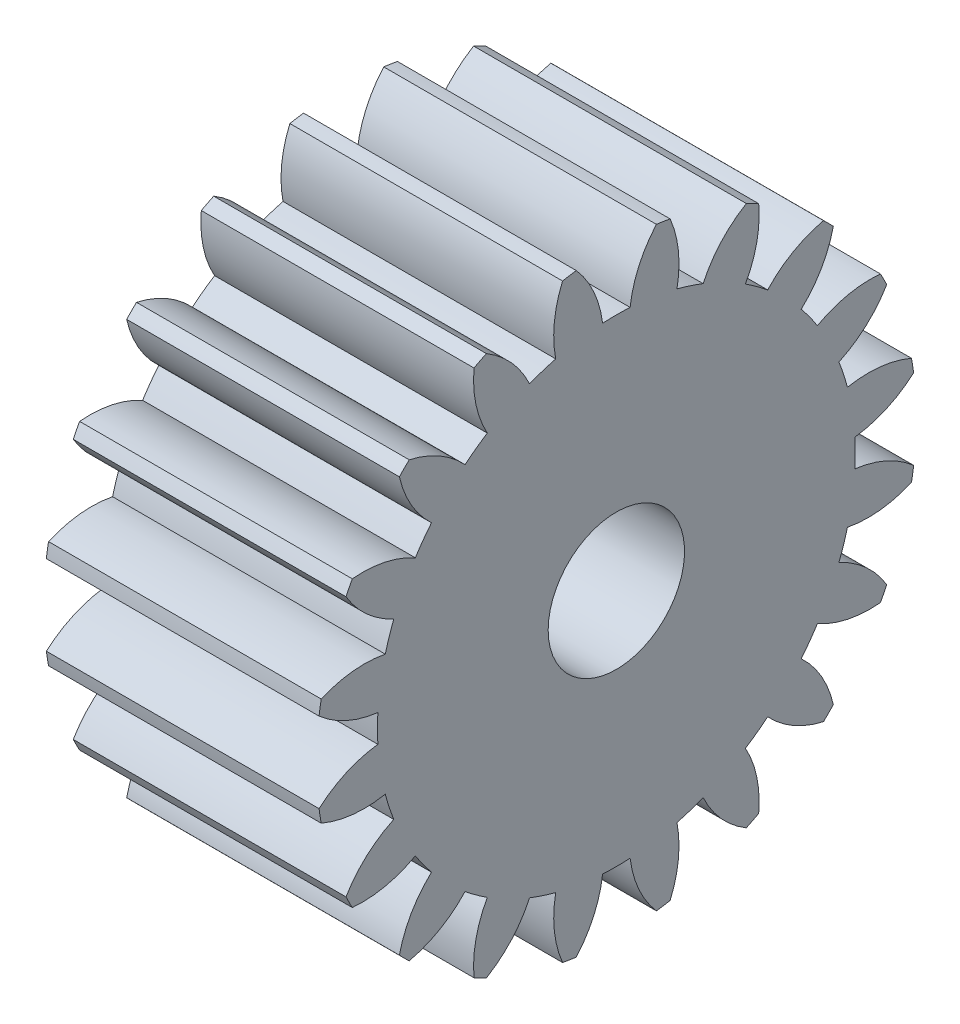
SolidWorks part; units mm, degrees
ref_plane "Plane1" through (0, 0, 0) normal (0, 0, 1) x (1, 0, 0)
ref_plane "Plane2" through (0, 0, 0) normal (0, 1, 0) x (1, 0, 0)
ref_plane "Plane3" through (0, 0, 0) normal (1, 0, 0) x (0, 0, -1)
sketch "HoldingSke" plane through (0, 0, 0) normal (0, 1, 0) x (1, 0, 0)
  line L0 (0, 0) -> (477.3639, -173.7462)
  line L1 (-15, 0) -> (100, 0) construction
  line L2 (0, 0) -> (-2.1039, 2.3779)
  line L3 (0, 0) -> (-11.863, 4.5341)
  line L4 (0, 0) -> (8.1152, 2.9537)
  line L5 (0, 0) -> (-47.5972, -17.7524)
  line L6 (0, 0) -> (-10.5278, -7.1032)
  line L7 (-2.1039, 2.3779) -> (8.8308, 51.9871)
  line L8 (-76.2, 54.61) -> (-69.596, 54.61)
  line L9 (-71.009, 38.7566) -> (-53.1078, 45.2721)
  line L10 (-76.2, 71.12) -> (104.1128, 71.12)
  line L11 (0, 0) -> (-12.7, 0)
  line L12 (-76.2, 101.6) -> (-76.1492, 101.6)
  line L13 (24.9733, 27.94) -> (52.9518, 28.4284)
  line L14 (24.9733, 27.94) -> (25.0241, 27.9398)
  line L15 (24.9733, 27.94) -> (100.4021, 29.52)
  circle A0 centre (0, 0) radius 3.175
  circle A1 centre (0, 0) radius 11.1252
  circle A2 centre (0, 0) radius 38.1
  circle A3 centre (0, 0) radius 3.175
  dimension "Hub_dia" = 76.2
  dimension "Pitch" = 508
  dimension "Overall_len" = 50.8
  dimension "OAL" = 50.8001
  dimension "Ap" = 20
  dimension "H" = 19.05
  dimension "Pitch_radius" = 180.3128
  dimension "Backlash" = 0.0508
  dimension "Addendum_fac" = 1
  dimension "Dedendum_fac" = 1.2
  dimension "Clearance_fac" = 0.2
  dimension "Dedendum_add" = 0.0508
sketch "BasProSke" plane through (0, 0, 0) normal (0, 1, 0) x (1, 0, 0)
  line L0 (-10, 0) -> (60, 0) construction
  line L1 (0, 0) -> (0, 13.97)
  line L2 (0, 0) -> (12.7, 0)
  line L3 (12.7, 0) -> (12.7, 13.97)
  line L4 (12.7, 13.97) -> (0, 13.97)
revolve "Base-Revolve" add sketch "BasProSke" angle 360 about L0
sketch "TooCutSke" plane through (0, 0, 0) normal (1, 0, 0) x (0, 0, -1)
  line L1 (0, 0) -> (0, 107) construction
  line L2 (0, 0) -> (-1.0853, 12.6535) construction
  line L3 (0, 0) -> (-3.9633, 25.0231) construction
  line L4 (-1.0853, 12.6535) -> (-1.9816, 12.5116) construction
  arc A0 (0.6405, 11.1067) -> (-0.6405, 11.1067) centre (0, 0) ccw
  arc A1 (1.8856, 13.8678) -> (-1.8856, 13.8678) centre (0, 0) ccw
  circle A2 centre (0, 0) radius 12.7 construction
  circle A3 centre (0, 0) radius 11.9341 construction
  arc A4 (-0.6405, 11.1067) -> (-1.8856, 13.8678) centre (-5.6834, 10.4939) ccw
  arc A5 (1.8856, 13.8678) -> (0.6405, 11.1067) centre (5.6834, 10.4939) ccw
extrude "ToothCut" cut sketch "TooCutSke" along normal through all
fillet "Breaks" [suppressed] radius 0.0254
fillet "RootFillets" [suppressed] radius 0.3048
pattern_circular "TeethCuts" count 20 every 18 about axis through (-10, 0, 0) along (1, 0, 0) of "ToothCut", "RootFillets", "Breaks"
sketch "HubNeaOneSke" plane through (0, 0, 0) normal (-1, 0, 0) x (0, 0, 1)
  circle A0 centre (0, 0) radius 11.1252
extrude "HubNearOne" [suppressed] add sketch "HubNeaOneSke" along normal blind 38.1001
sketch "HubNeaBotSke" plane through (0, 0, 0) normal (-1, 0, 0) x (0, 0, 1)
  circle A0 centre (0, 0) radius 11.1252
extrude "HubNearBoth" [suppressed] add sketch "HubNeaBotSke" along normal blind 19.05
ref_plane "FarPln" through (12.7, 0, 0) normal (1, 0, 0) x (0, 0, -1)
sketch "HubFarSke" plane through (12.7, 0, 0) normal (1, 0, 0) x (0, 0, -1)
  circle A0 centre (0, 0) radius 11.1252
extrude "HubFar" [suppressed] add sketch "HubFarSke" along normal blind 19.05
sketch "BorSke" plane through (0, 0, 0) normal (1, 0, 0) x (0, 0, -1)
  circle A0 centre (0, 0) radius 3.175
extrude "Bore" cut sketch "BorSke" along normal mid plane 101.6001
sketch "KeySke" plane through (0, 0, 0) normal (1, 0, 0) x (0, 0, -1)
  line L0 (-0.127, 0) -> (-0.127, 3.429)
  line L1 (-0.127, 3.429) -> (0.127, 3.429)
  line L2 (0.127, 3.429) -> (0.127, 0)
  line L3 (0, 0) -> (0, 34) construction
  line L4 (-0.127, 0) -> (0.127, 0)
  dimension "Width" = 0.254
extrude "Keyway" [suppressed] cut sketch "KeySke" along normal mid plane 101.6001
pattern_circular "Keyway2" [suppressed] count 2 every 90 about axis through (-10, 0, 0) along (1, 0, 0)
equation "' \"Pitch@HoldingSke\" = 4"
equation "' \"Num_teeth@HoldingSke\" = 12"
equation "' \"Ap@HoldingSke\" =  20"
equation "' \"Ap@HoldingSke\" = 20"
equation "' \"Width@HoldingSke\" = 0.5"
equation "' \"Hub_dia@HoldingSke\"= 1"
equation "' \"Hub_dia@HoldingSke\" = 1"
equation "' \"Overall_len@HoldingSke\" = 1.0"
equation "' \"Bore@HoldingSke\" = 0.75"
equation "' \"T_dim@HoldingSke\" = 0.85"
equation "' \"Width@KeySke\" = 0.25"
equation "' \"Show_teeth@HoldingSke\" = 13"
equation "' \"Backlash@HoldingSke\" = 0.009"
equation "' \"Addendum_fac@HoldingSke\" = 1.0"
equation "' \"Dedendum_fac@HoldingSke\" = 1.25"
equation "' \"Dedendum_add@HoldingSke\" = 0.00005"
equation "' \"Clearance_fac@HoldingSke\" = 0.25"
equation "' \"Pitch@HoldingSke\" = 0.5"
equation "' \"Num_teeth@HoldingSke\" = 23"
equation "' \"Show_teeth@HoldingSke\" = 23"
equation "' \"Backlash@HoldingSke\" = 0.0375"
equation "\"Overcut_dia@TooCutSke\" = (\"Num_teeth@HoldingSke\" + 2 * \"Addendum_fac@HoldingSke\") / \"Pitch@HoldingSke\" + 0.002"
equation "\"Pitch_dia@TooCutSke\" = \"Num_teeth@HoldingSke\" / \"Pitch@HoldingSke\""
equation "\"Base_dia@TooCutSke\" = \"Num_teeth@HoldingSke\" / \"Pitch@HoldingSke\" * cos((\"Ap@HoldingSke\"  * 3.14159265 / 180))"
equation "\"Root_dia@TooCutSke\" = (\"Num_teeth@HoldingSke\" + 2) / \"Pitch@HoldingSke\" - 2 * (\"Addendum_fac@HoldingSke\" + \"Dedendum_fac@HoldingSke\") / \"Pitch@HoldingSke\" - \"Dedendum_add@HoldingSke\" * 2"
equation "\"Half_ang@TooCutSke\" = 180 / \"Num_teeth@HoldingSke\""
equation "\"Half_CT@TooCutSke\" = \"Num_teeth@HoldingSke\" / \"Pitch@HoldingSke\" * sin((3.14159265 / 2 / \"Num_teeth@HoldingSke\")) / 2 - 7 * \"Backlash@HoldingSke\" / 4"
equation "\"Flank_rad@TooCutSke\" = \"Num_teeth@HoldingSke\" / \"Pitch@HoldingSke\" / 5"
equation "\"Radius@RootFillets\" = \"Clearance_fac@HoldingSke\" / \"Pitch@HoldingSke\" + \"Dedendum_add@HoldingSke\""
equation "\"Break_rad@Breaks\" = 0.02 / \"Pitch@HoldingSke\""
equation "\"Thickness@HoldingSke\" = \"Width@HoldingSke\""
equation "\"OAL@HoldingSke\" = \"Thickness@HoldingSke\""
equation "\"MHD@HoldingSke\" = (\"Num_teeth@HoldingSke\" + 2) / \"Pitch@HoldingSke\" - 2 * (\"Addendum_fac@HoldingSke\" + \"Dedendum_fac@HoldingSke\")  / \"Pitch@HoldingSke\" - \"Dedendum_add@HoldingSke\" * 2"
equation "\"MBD@HoldingSke\" = (\"Num_teeth@HoldingSke\" + 2) / \"Pitch@HoldingSke\" - 2 * (\"Addendum_fac@HoldingSke\" + \"Dedendum_fac@HoldingSke\")  / \"Pitch@HoldingSke\" - \"Dedendum_add@HoldingSke\" * 2 - 0.002"
equation "\"MHD@HoldingSke\" = ((sgn( \"MHD@HoldingSke\" - \"Hub_dia@HoldingSke\" )-1)*( \"MHD@HoldingSke\" - \"Hub_dia@HoldingSke\" ))/-2+ \"Hub_dia@HoldingSke\""
equation "\"MBD@HoldingSke\" = ((sgn( \"MBD@HoldingSke\" - \"Bore@HoldingSke\" )-1)*( \"MBD@HoldingSke\" - \"Bore@HoldingSke\" ))/-2+ \"Bore@HoldingSke\""
equation "\"OAL@HoldingSke\" = ((sgn( \"OAL@HoldingSke\" - \"Overall_len@HoldingSke\" )+1)*( \"OAL@HoldingSke\" - \"Overall_len@HoldingSke\" ))/2 + \"Overall_len@HoldingSke\" + 0.000002"
equation "\"Num_teeth@TeethCuts\" = int( \"Show_teeth@HoldingSke\" ) + 1"
equation "\"Num_teeth@TeethCuts\" = ((sgn( \"Num_teeth@TeethCuts\" - \"Num_teeth@HoldingSke\" )-1)*( \"Num_teeth@TeethCuts\" - \"Num_teeth@HoldingSke\" ))/-2+ \"Num_teeth@HoldingSke\""
equation "\"Num_teeth@TeethCuts\" = ((sgn( \"Num_teeth@TeethCuts\" - 2.0)+1)*( \"Num_teeth@TeethCuts\" - 2.0))/2 +2.0"
equation "\"Angle@TeethCuts\" = 360.0 / \"Num_teeth@HoldingSke\""
equation "\"Diameter@BasProSke\" = (\"Num_teeth@HoldingSke\" + 2 * \"Addendum_fac@HoldingSke\") / \"Pitch@HoldingSke\""
equation "\"Thickness@BasProSke\"  = \"Thickness@HoldingSke\""
equation "' \"Fillet_rad@BasProSke\" =  \"Thickness@HoldingSke\" * 0.05"
equation "' \"Fillet_rad@BasProSke\" = \"Thickness@HoldingSke\" * 0.05"
equation "\"MHD@HoldingSke\" = ((sgn( \"MHD@HoldingSke\" - \"Root_dia@TooCutSke\" )-1)*( \"MHD@HoldingSke\" - \"Root_dia@TooCutSke\" ))/-2+ \"Root_dia@TooCutSke\""
equation "\"Diameter@HubNeaOneSke\" = \"MHD@HoldingSke\""
equation "\"Length@HubNearOne\" = \"OAL@HoldingSke\" - \"Thickness@BasProSke\""
equation "\"Diameter@HubNeaBotSke\" = \"MHD@HoldingSke\""
equation "\"Length@HubNearBoth\" = ( \"OAL@HoldingSke\" - \"Thickness@BasProSke\" ) / 2.0"
equation "\"Thickness@FarPln\" = \"Thickness@BasProSke\""
equation "\"Diameter@HubFarSke\" = \"MHD@HoldingSke\""
equation "\"Length@HubFar\" = ( \"OAL@HoldingSke\" - \"Thickness@BasProSke\" ) / 2.0"
equation "\"Diameter@BorSke\" = \"MBD@HoldingSke\""
equation "\"D1@Bore\" = \"OAL@HoldingSke\" * 2.0"
equation "\"D1@Keyway\" = \"OAL@HoldingSke\" * 2.0"
equation "\"Offset@KeySke\" = \"T_dim@HoldingSke\" - \"MBD@HoldingSke\" / 2.0"
